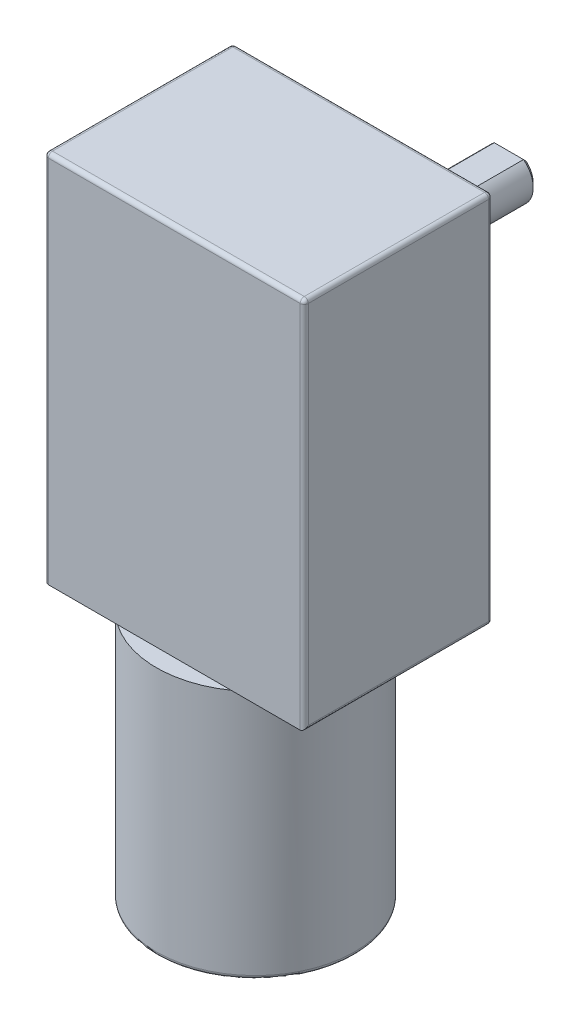
SolidWorks part; units mm, degrees
material "AISI 1020"
ref_plane "Спереди" through (0, 0, 0) normal (0, 0, 1) x (1, 0, 0)
ref_plane "Сверху" through (0, 0, 0) normal (0, 1, 0) x (1, 0, 0)
ref_plane "Справа" through (0, 0, 0) normal (1, 0, 0) x (0, 0, -1)
sketch "Эскиз1" plane through (0, 0, 0) normal (0, 1, 0) x (1, 0, 0)
  circle A0 centre (0, 0) radius 3.5
  dimension "D1" = 7
extrude "Бобышка-Вытянуть1" add sketch "Эскиз1" along normal blind 3
sketch "Эскиз2" plane through (0, 3, 0) normal (0, 1, 0) x (1, 0, 0)
  circle A0 centre (0, 0) radius 12.2
  dimension "D1" = 24.4
extrude "Бобышка-Вытянуть2" add sketch "Эскиз2" along normal blind 30.8
sketch "Эскиз3" plane through (0, 33.8, 0) normal (0, 1, 0) x (1, 0, 0)
  line L0 (0, 0) -> (2.2217, 0) construction
  line L1 (-16, 15.2) -> (16, 15.2)
  line L2 (-16, 15.2) -> (-16, -10)
  line L3 (-16, -10) -> (16, -10)
  line L4 (16, 15.2) -> (16, -10)
  point P5 (0, -10)
  dimension "D1" = 25.2
  dimension "D2" = 32
  dimension "D3" = 10
extrude "Бобышка-Вытянуть3" add sketch "Эскиз3" along normal blind 46
sketch "Эскиз4" plane through (0, 0, -15.2) normal (0, 0, -1) x (-1, 0, 0)
  line L0 (0, 79.8) -> (0, 53.9336) construction
  line L1 (-16, 79.8) -> (16, 79.8) construction
  circle A0 centre (0, 64.8) radius 3
  dimension "D2" = 6
  dimension "D1" = 15
extrude "Бобышка-Вытянуть4" add sketch "Эскиз4" along normal blind 16.5
sketch "Эскиз5" plane through (0, 0, -31.7) normal (0, 0, -1) x (-1, 0, 0)
  line L0 (-1.8, 67.2) -> (1.8, 67.2)
  circle A1 centre (0, 64.8) radius 3
  arc A2 (1.8, 67.2) -> (-1.8, 67.2) centre (0, 64.8) ccw
  dimension "D2" = 2.4
  dimension "D1" = 0
extrude "Вырез-Вытянуть1" cut sketch "Эскиз5" against normal blind 12
sketch "Эскиз6" plane through (0, 0, -15.2) normal (0, 0, -1) x (-1, 0, 0)
  line L0 (0, 64.8) -> (0, 84.2537) construction
  line L1 (-4.1679, 52.8) -> (4.1679, 52.8) construction
  line L2 (-4.1679, 55.8) -> (4.1679, 55.8)
  line L3 (-4.1679, 49.8) -> (4.1679, 49.8)
  line L4 (-16, 33.8) -> (16, 33.8)
  line L5 (16, 33.8) -> (16, 79.8)
  line L6 (16, 79.8) -> (-16, 79.8)
  line L7 (-16, 79.8) -> (-16, 33.8)
  line L8 (-16, 33.8) -> (16, 33.8)
  line L9 (16, 33.8) -> (16, 79.8)
  line L10 (16, 79.8) -> (-16, 79.8)
  line L11 (-16, 79.8) -> (-16, 33.8)
  circle A0 centre (9, 73.8) radius 3
  circle A1 centre (-9, 73.8) radius 3
  circle A2 centre (-9, 40.8) radius 3
  circle A3 centre (9, 40.8) radius 3
  circle A4 centre (0, 64.8) radius 6.5
  circle A5 centre (0, 64.8) radius 3
  arc A6 (-4.1679, 55.8) -> (-4.1679, 49.8) centre (-4.1679, 52.8) ccw
  arc A7 (4.1679, 49.8) -> (4.1679, 55.8) centre (4.1679, 52.8) ccw
  point P19 (0, 52.8)
  line M16 (-16, 33.8) -> (16, 33.8)
  line M17 (16, 33.8) -> (16, 79.8)
  line M18 (16, 79.8) -> (-16, 79.8)
  line M19 (-16, 79.8) -> (-16, 33.8)
  dimension "D4" = 6
  dimension "D7" = 6
  dimension "D8" = 13
  dimension "D10" = 3
  dimension "D2" = 18
  dimension "D3" = 6
  dimension "D5" = 18
  dimension "D6" = 33
  dimension "D9" = 12
  dimension "D1" = 0
extrude "Вырез-Вытянуть2" cut sketch "Эскиз6" against normal blind 2 contours A7 L3 A6 L2 A4 A3 A2 A1 A0 M19 M16 M17 M18
fillet "Скругление1" radius 0.5 10 edges at (7.1679, 52.8, -15.2) (0, 49.8, -15.2) (-7.1679, 52.8, -15.2) (6, 40.8, -15.2) (-6.5, 64.8, -15.2) (-6.5, 64.8, -13.2) (-12, 40.8, -13.2) (-12, 73.8, -15.2) (6, 73.8, -15.2) (0, 55.8, -15.2)
chamfer "Фаска1" distance 0.5 angle 45 1 edges at (0, 61.8, -31.7)
chamfer "Фаска2" distance 0.5 angle 45 1 edges at (0, 67.2, -31.7)
sketch "Эскиз7" plane through (0, 0, -15.2) normal (0, 0, -1) x (-1, 0, 0)
  circle A0 centre (9, 73.8) radius 1.6
  circle A1 centre (-9, 73.8) radius 1.6
  circle A2 centre (-9, 40.8) radius 1.6
  circle A3 centre (9, 40.8) radius 1.6
  dimension "D1" = 3.2
extrude "Вырез-Вытянуть3" cut sketch "Эскиз7" against normal blind 4
fillet "Скругление2" radius 0.5 13 edges at (-16, 79.8, -1.6) (-16, 56.8, 10) (-16, 33.8, -1.6) (-16, 56.8, -13.2) (0, 0, 3.5) (0, 3, 12.2) (16, 33.8, -1.6) (16, 56.8, 10) (16, 56.8, -13.2) (0, 33.8, -13.2) (0, 79.8, 10) (0, 79.8, -13.2) (16, 79.8, -1.6)
